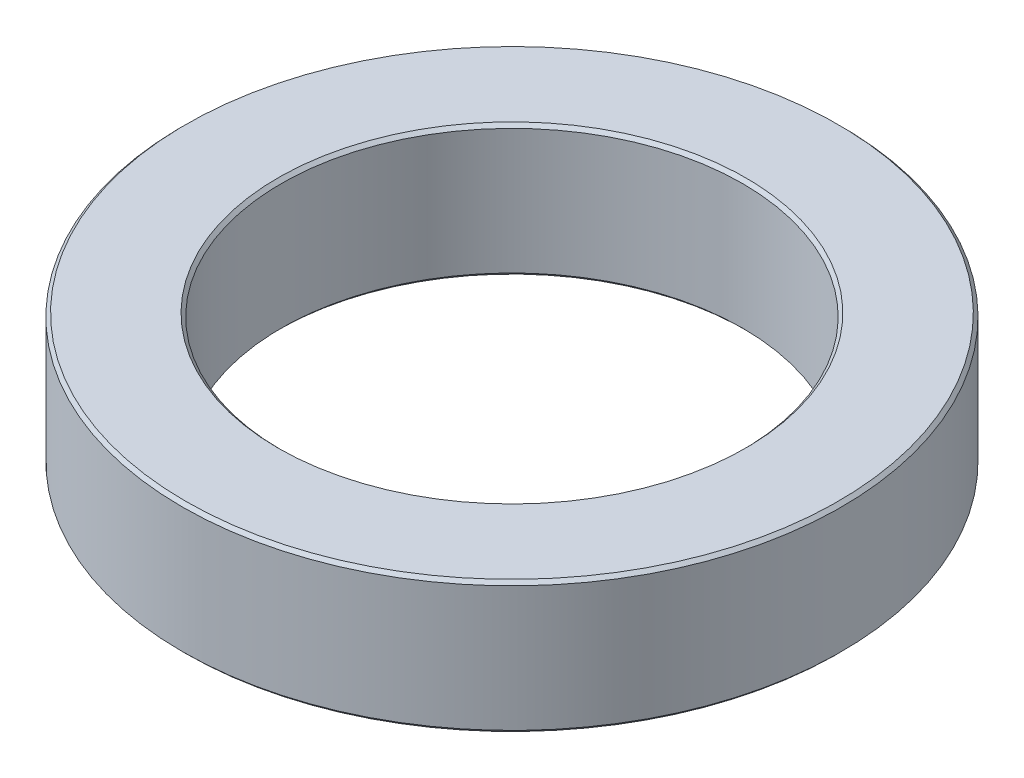
SolidWorks part; units mm, degrees
ref_plane "Front Plane" through (0, 0, 0) normal (0, 0, 1) x (1, 0, 0)
ref_plane "Top Plane" through (0, 0, 0) normal (0, 1, 0) x (1, 0, 0)
ref_plane "Right Plane" through (0, 0, 0) normal (1, 0, 0) x (0, 0, -1)
sketch "Sketch1" plane through (0, 0, 0) normal (0, 1, 0) x (1, 0, 0)
  circle A0 centre (0, 0) radius 14
  circle A1 centre (0, 0) radius 20
  dimension "D1" = 28
  dimension "D2" = 40
extrude "Boss-Extrude1" add sketch "Sketch1" along normal mid plane 8
chamfer "Chamfer1" distance 0.2 angle 45 4 edges at (0, 4, 14) (0, 4, 20) (0, -4, 14) (0, -4, 20)
